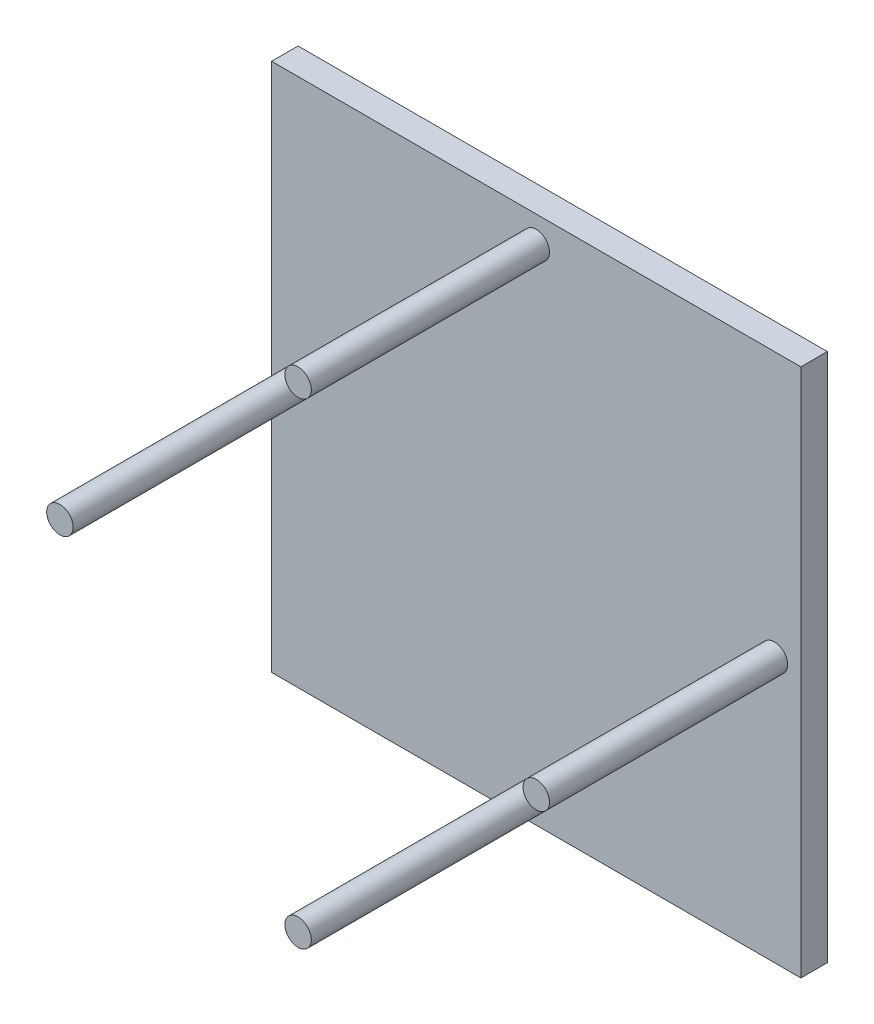
SolidWorks part; units mm, degrees
ref_plane "Front Plane" through (0, 0, 0) normal (0, 0, 1) x (1, 0, 0)
ref_plane "Top Plane" through (0, 0, 0) normal (0, 1, 0) x (1, 0, 0)
ref_plane "Right Plane" through (0, 0, 0) normal (1, 0, 0) x (0, 0, -1)
sketch "Sketch1" plane through (0, 0, 0) normal (0, 0, 1) x (1, 0, 0)
  line L1 (0, 0) -> (200, 0)
  line L2 (0, 0) -> (0, 200)
  line L3 (0, 200) -> (200, 200)
  line L4 (200, 0) -> (200, 200)
  dimension "D1" = 200
extrude "Boss-Extrude1" add sketch "Sketch1" along normal blind 10
sketch "Sketch2" plane through (0, 0, 0) normal (0, 0, -1) x (-1, 0, 0)
  circle A0 centre (-100, 100) radius 98.8367 construction
sketch "Sketch3" plane through (0, 0, 0) normal (0, 0, -1) x (-1, 0, 0)
  line L0 (-200, 0) -> (0, 200) construction
  line L1 (-200, 200) -> (0, 0) construction
sketch "Sketch4" plane through (0, 0, 0) normal (0, 0, -1) x (-1, 0, 0)
  circle A0 centre (-100, 100) radius 90 construction
  circle A1 centre (-190, 100) radius 5
  circle A2 centre (-100, 10) radius 5
  circle A3 centre (-100, 190) radius 5
  circle A4 centre (-10, 100) radius 5
  dimension "D1" = 180
  dimension "D2" = 10
extrude "Boss-Extrude2" add sketch "Sketch4" against normal blind 100
equation "\"D1@Sketch1\"=200"
equation "\"D1@Boss-Extrude1\" =10"
equation "\"D1@Sketch4\" = \"D1@Sketch1\"-20"
